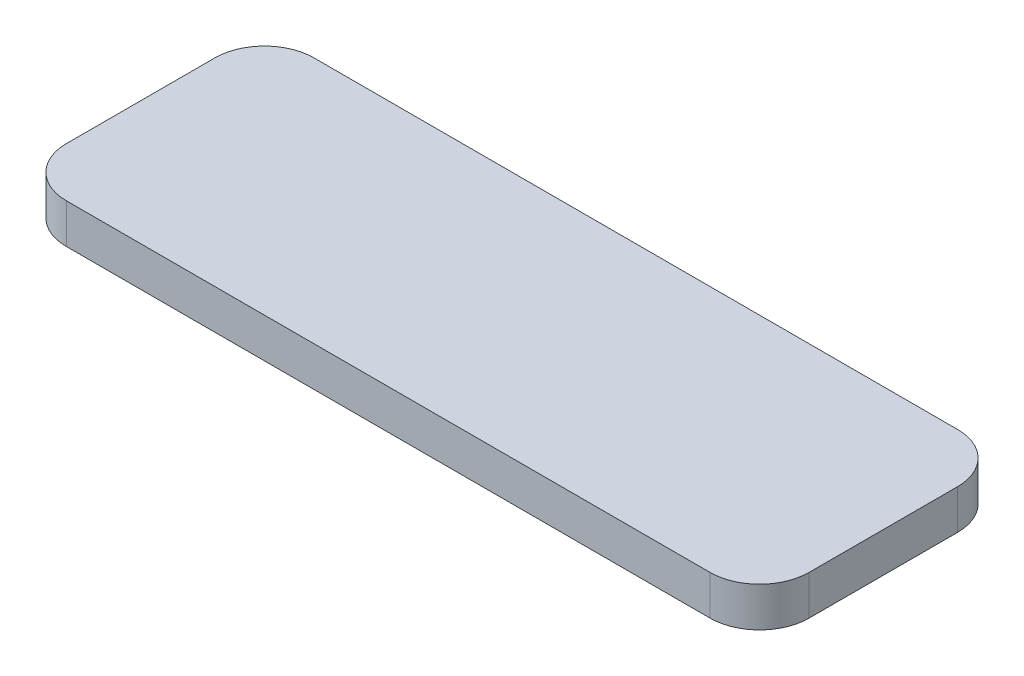
SolidWorks part; units mm, degrees
ref_plane "Front Plane" through (0, 0, 0) normal (0, 0, 1) x (1, 0, 0)
ref_plane "Top Plane" through (0, 0, 0) normal (0, 1, 0) x (1, 0, 0)
ref_plane "Right Plane" through (0, 0, 0) normal (1, 0, 0) x (0, 0, -1)
sketch "Sketch1" plane through (0, 0, 0) normal (0, 1, 0) x (1, 0, 0)
  line L1 (-33.0811, 49.6458) -> (96.9189, 49.6458)
  line L2 (-43.0811, 39.6458) -> (-43.0811, 9.6458)
  line L3 (-33.0811, -0.3542) -> (96.9189, -0.3542)
  line L4 (106.9189, 39.6458) -> (106.9189, 9.6458)
  arc A0 (-33.0811, 49.6458) -> (-43.0811, 39.6458) centre (-33.0811, 39.6458) ccw
  arc A1 (96.9189, 49.6458) -> (106.9189, 39.6458) centre (96.9189, 39.6458) cw
  arc A2 (96.9189, -0.3542) -> (106.9189, 9.6458) centre (96.9189, 9.6458) ccw
  arc A3 (-43.0811, 9.6458) -> (-33.0811, -0.3542) centre (-33.0811, 9.6458) ccw
  point P6 (-43.0811, 49.6458)
  point P9 (106.9189, 49.6458)
  point P12 (106.9189, -0.3542)
  dimension "D3" = 10
  dimension "D4" = 10
  dimension "D5" = 10
  dimension "D6" = 10
  dimension "D1" = 150
  dimension "D2" = 50
extrude "Boss-Extrude1" add sketch "Sketch1" along normal blind 8 contours L1 A1 L4 A2 L3 A3 L2 A0
